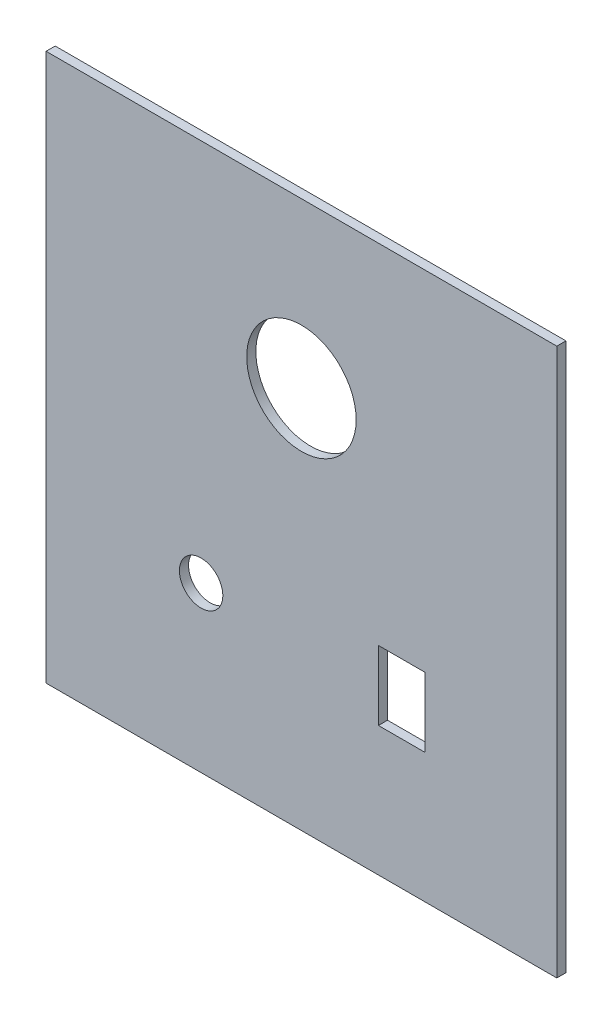
SolidWorks part; units mm, degrees
ref_plane "Alzado" through (0, 0, 0) normal (0, 0, 1) x (1, 0, 0)
ref_plane "Planta" through (0, 0, 0) normal (0, 1, 0) x (1, 0, 0)
ref_plane "Vista lateral" through (0, 0, 0) normal (1, 0, 0) x (0, 0, -1)
sketch "Croquis1" plane through (0, 0, 0) normal (0, 0, 1) x (1, 0, 0)
  line L0 (-27.5, -30) -> (27.5, -30) construction
  line L1 (-70, -75) -> (70, -75)
  line L2 (-70, -75) -> (-70, 75)
  line L3 (-70, 75) -> (70, 75)
  line L4 (70, -75) -> (70, 75)
  line L5 (-70, -75) -> (70, 75) construction
  line L6 (-70, 75) -> (70, -75) construction
  line L7 (21.1, -20.5) -> (33.9, -20.5)
  line L8 (21.1, -20.5) -> (21.1, -39.5)
  line L9 (21.1, -39.5) -> (33.9, -39.5)
  line L10 (33.9, -20.5) -> (33.9, -39.5)
  line L11 (21.1, -20.5) -> (33.9, -39.5) construction
  line L12 (21.1, -39.5) -> (33.9, -20.5) construction
  circle A0 centre (0, 30) radius 15
  circle A1 centre (-27.5, -30) radius 5.95
  point P0 (0, 0)
  point P8 (27.5, -30)
  point P15 (0, 0)
  point P17 (0, -30)
  point P18 (0, 0)
  dimension "D3" = 30
  dimension "D6" = 11.9
  dimension "D1" = 140
  dimension "D2" = 150
  dimension "D4" = 19
  dimension "D5" = 12.8
  dimension "D7" = 30
  dimension "D8" = 30
  dimension "D9" = 55
extrude "Saliente-Extruir1" add sketch "Croquis1" along normal blind 2.5 contours L1 L4 L3 L2 A1 A0 L7 L10 L9 L8
